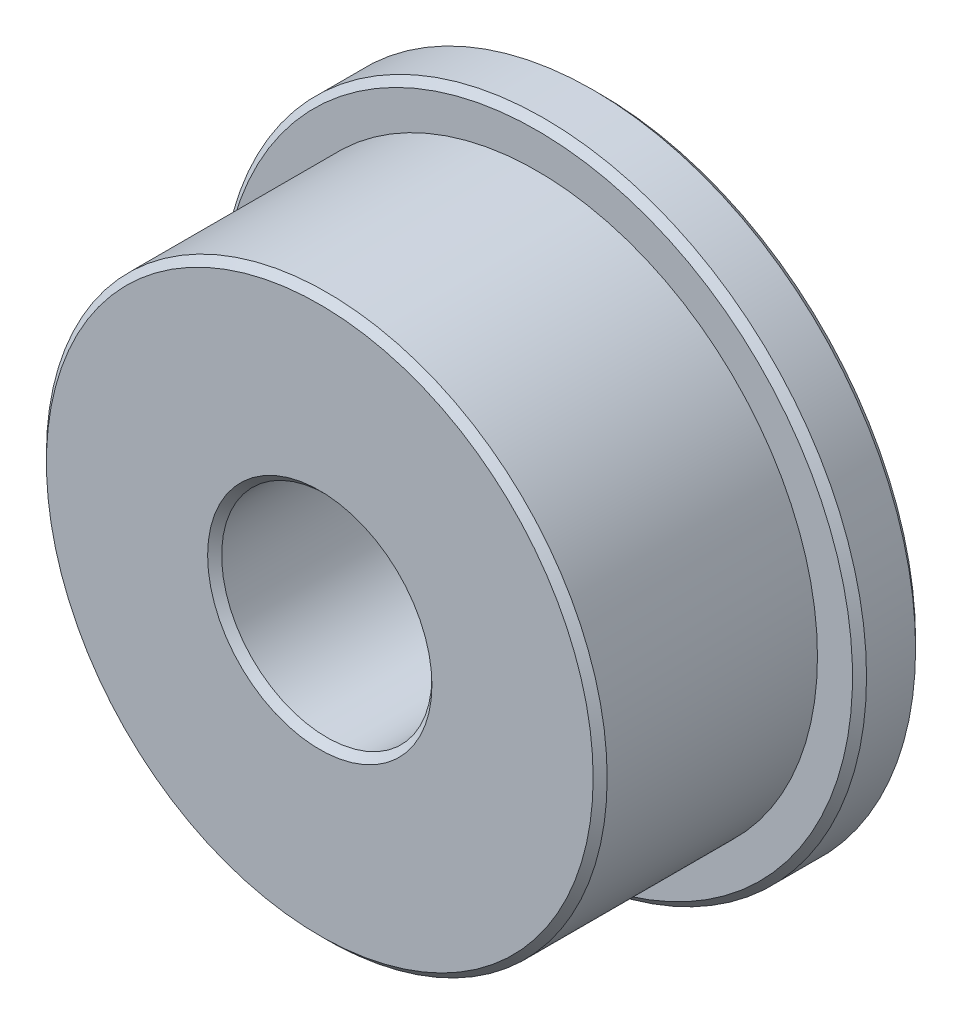
SolidWorks part; units mm, degrees
ref_plane "前视基准面" through (0, 0, 0) normal (0, 0, 1) x (1, 0, 0)
ref_plane "上视基准面" through (0, 0, 0) normal (0, 1, 0) x (1, 0, 0)
ref_plane "右视基准面" through (0, 0, 0) normal (1, 0, 0) x (0, 0, -1)
sketch "草图1" plane through (0, 0, 0) normal (0, 0, 1) x (1, 0, 0)
  circle A0 centre (0, 0) radius 4
  circle A1 centre (0, 0) radius 1.5
  dimension "D1" = 3
  dimension "D2" = 8
extrude "凸台-拉伸1" add sketch "草图1" along normal mid plane 4
sketch "草图2" plane through (0, 0, -2) normal (0, 0, -1) x (-1, 0, 0)
  circle A0 centre (0, 0) radius 4.6
  circle A1 centre (0, 0) radius 4 construction
  circle A2 centre (0, 0) radius 4
  dimension "D1" = 9.2
extrude "凸台-拉伸2" add sketch "草图2" against normal blind 0.9
chamfer "倒角1" distance 0.1 angle 45 5 edges at (1.5, 0, -2) (1.5, 0, 2) (4, 0, 2) (-4.6, 0, -1.1) (-4.6, 0, -2)
